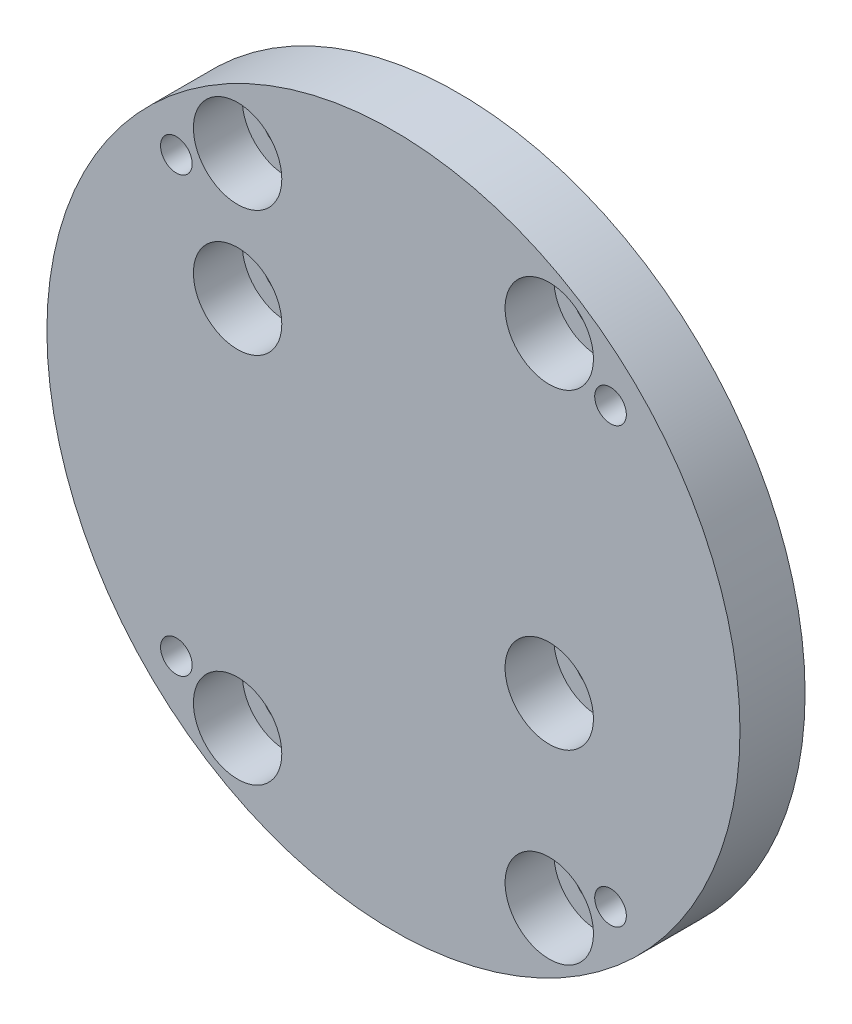
SolidWorks part; units mm, degrees
ref_plane "前视基准面" through (0, 0, 0) normal (0, 0, 1) x (1, 0, 0)
ref_plane "上视基准面" through (0, 0, 0) normal (0, 1, 0) x (1, 0, 0)
ref_plane "右视基准面" through (0, 0, 0) normal (1, 0, 0) x (0, 0, -1)
sketch "草图1" plane through (0, 0, 0) normal (0, 0, 1) x (1, 0, 0)
  circle A0 centre (0, 0) radius 74.5
  dimension "D1" = 149
extrude "凸台-拉伸1" add sketch "草图1" along normal blind 14
hole_wizard "M10 六角头螺栓的柱形沉头孔1" positions "草图3" profile "草图2" counterbore size "M10" standard "GB" end condition through all
sketch "草图3" plane through (0, 0, 14) normal (0, 0, 1) x (1, 0, 0)
  line L0 (0, 74.5) -> (0, -74.5) construction
  line L2 (-74.5, 0) -> (74.5, 0) construction
  circle A0 centre (0, 0) radius 74.5 construction
  point P0 (-33.5, 26.5)
  point P2 (-33.5, -53.5)
  point P4 (33.5, -53.5)
  point P6 (33.5, -13.5)
  point P8 (33.5, 53.5)
  point P10 (-33.5, 53.5)
  dimension "D1" = 33.5
  dimension "D2" = 33.5
  dimension "D3" = 33.5
  dimension "D4" = 53.5
  dimension "D5" = 27
  dimension "D6" = 53.5
  dimension "D7" = 33.5
  dimension "D8" = 13.5
  dimension "D9" = 40
  dimension "D10" = 33.5
  dimension "D11" = 33.5
  dimension "D12" = 53.5
sketch "草图2" plane through (-33.5, 26.5, 14) normal (1, 0, 0) x (0, -1, 0)
  line L0 (0, 0) -> (0, 14)
  line L1 (0, 14) -> (5.5, 14)
  line L3 (5.5, 14) -> (5.5, 10.5)
  line L4 (5.5, 10.5) -> (9.5, 10.5)
  line L5 (9.5, 10.5) -> (9.5, 0)
  line L7 (9.5, 0) -> (0, 0)
  line L11 (0, -6.35) -> (0, 107.95) construction
  dimension "通孔孔直径" = 11
  dimension "通孔孔深度" = 14
  dimension "柱形沉头孔直径" = 19
  dimension "柱形沉头孔深度" = 10.5
hole_wizard "M8 螺纹孔的螺纹孔钻头1" positions "草图7" profile "草图6" hole size "M8" standard "GB" end condition through all
sketch "草图7" plane through (0, 0, 14) normal (0, 0, 1) x (1, 0, 0)
  line L0 (0, 0) -> (46.669, 46.669) construction
  line L2 (0, 0) -> (0, 74.5) construction
  circle A0 centre (0, 0) radius 66 construction
  circle A1 centre (0, 0) radius 74.5 construction
  point P0 (46.669, 46.669)
  dimension "D1" = 132
  dimension "D2" = 45
sketch "草图6" plane through (46.669, 46.669, 14) normal (1, 0, 0) x (0, -1, 0)
  line L0 (0, 0) -> (0, 14)
  line L1 (0, 14) -> (3.4, 14)
  line L2 (3.4, 14) -> (3.4, 0)
  line L5 (3.4, 0) -> (0, 0)
  line L11 (0, -6.35) -> (0, 107.95) construction
  dimension "通孔孔直径" = 6.8
  dimension "通孔孔深度" = 14
pattern_circular "阵列(圆周)1" count 4 over 360 about axis through (0, 0, 0) along (0, 0, 1) of "M8 螺纹孔的螺纹孔钻头1"
